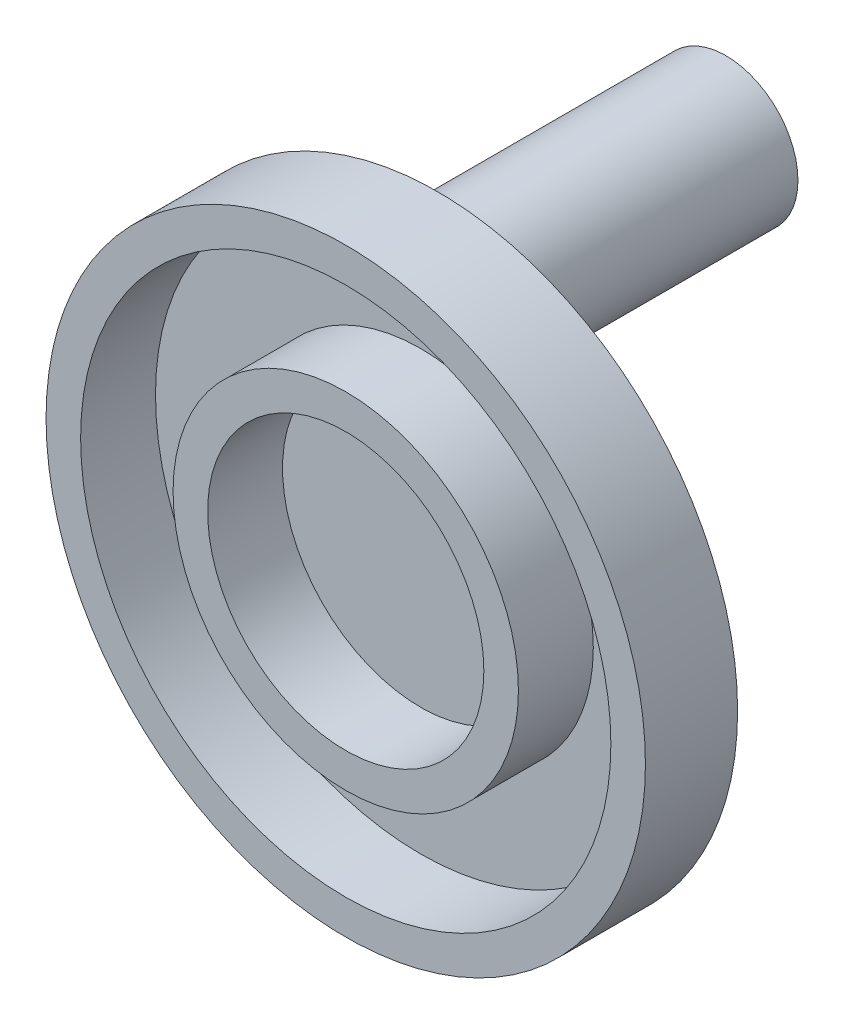
SolidWorks part; units mm, degrees
ref_plane "Front Plane" through (0, 0, 0) normal (0, 0, 1) x (1, 0, 0)
ref_plane "Top Plane" through (0, 0, 0) normal (0, 1, 0) x (1, 0, 0)
ref_plane "Right Plane" through (0, 0, 0) normal (1, 0, 0) x (0, 0, -1)
sketch "Sketch1" plane through (0, 0, 0) normal (0, 0, 1) x (1, 0, 0)
  circle A1 centre (0, 0) radius 12.5
  dimension "D1" = 25
extrude "Boss-Extrude1" add sketch "Sketch1" against normal blind 50
sketch "Sketch2" plane through (0, 0, 0) normal (0, 0, 1) x (1, 0, 0)
  line L0 (0, 0) -> (0, 3) construction
  line L3 (0, 3) -> (0, -35) construction
  circle A5 centre (0, -35) radius 38 construction
  circle A6 centre (0, -35) radius 46.025
  circle A7 centre (0, -35) radius 29.975
  circle A8 centre (0, -35) radius 52.025
  circle A9 centre (0, -35) radius 23.975
  dimension "D1" = 38
  dimension "D2" = 3
  dimension "D3" = 8.025
  dimension "D4" = 8.025
  dimension "D5" = 6
  dimension "D6" = 6
extrude "Boss-Extrude2" add sketch "Sketch2" along normal blind 16 contours A8 A6 | A7 A9
sketch "Sketch4" plane through (0, 0, 0) normal (0, 0, 1) x (1, 0, 0)
  circle A0 centre (0, -35) radius 52.025 construction
  circle A1 centre (0, -35) radius 52.025
extrude "Boss-Extrude3" add sketch "Sketch4" along normal blind 3
